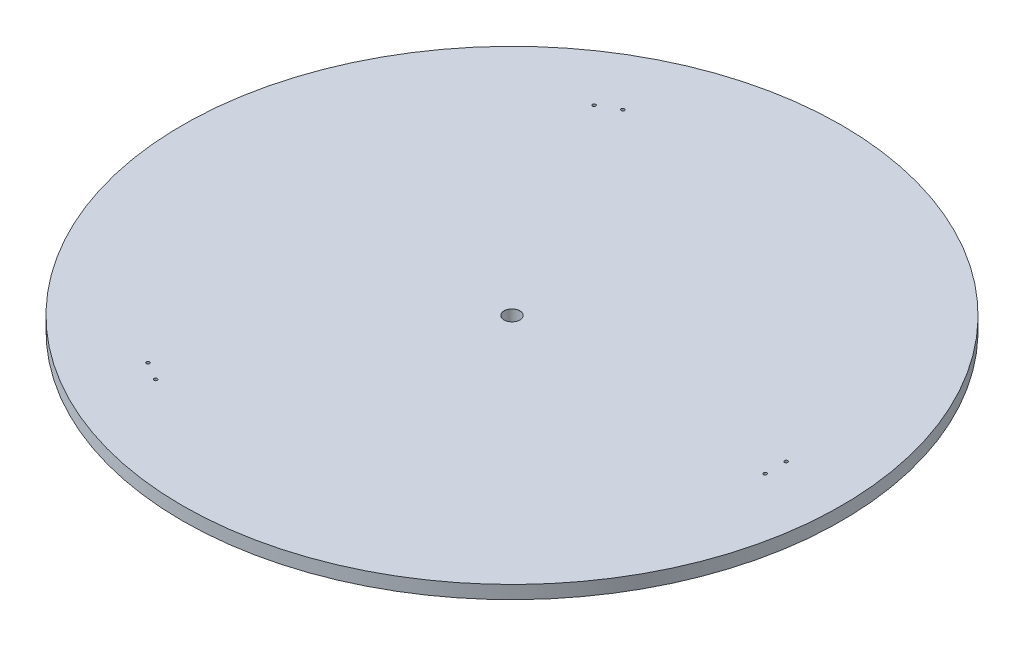
SolidWorks part; units mm, degrees
ref_plane "Plan de face" through (0, 0, 0) normal (0, 0, 1) x (1, 0, 0)
ref_plane "Plan de dessus" through (0, 0, 0) normal (0, 1, 0) x (1, 0, 0)
ref_plane "Plan de droite" through (0, 0, 0) normal (1, 0, 0) x (0, 0, -1)
sketch "Esquisse1" plane through (0, 0, 0) normal (0, 1, 0) x (1, 0, 0)
  circle A0 centre (0, 0) radius 250
  dimension "D1" = 500
extrude "Boss.-Extru.1" add sketch "Esquisse1" along normal mid plane 10
sketch "Esquisse5" plane through (0, 5, 0) normal (0, 1, 0) x (1, 0, 0)
  point P0 (0, 0)
hole_wizard "Dégagement M101" positions "Esquisse5" profile "Esquisse4" hole size "M10" standard "ISO" end condition through all
sketch "Esquisse4" plane through (0, 5, 0) normal (1, 0, 0) x (0, 0, 1)
  line L0 (0, 0) -> (0, 10)
  line L1 (0, 10) -> (6, 10)
  line L2 (6, 10) -> (6, 0.025)
  line L3 (6, 0.025) -> (6.025, 0)
  line L5 (6.025, 0) -> (0, 0)
  line L6 (-6, 0.025) -> (-6.025, 0) construction
  line L11 (0, -6.35) -> (0, 107.95) construction
  dimension "Diamètre du perçage jusqu'au prochain" = 12
  dimension "Profondeur du perçage jusqu'au prochain" = 10
  dimension "Diamètre du fraisage entrant" = 12.05
  dimension "Angle du fraisage entrant" = 90
sketch "Esquisse6" plane through (0, 5, 0) normal (0, 1, 0) x (1, 0, 0)
  line L0 (0, 0) -> (458.2969, 0) construction
  line L1 (0, 0) -> (-167.1022, 289.4294) construction
  line L2 (0, 0) -> (-171.7601, -297.4973) construction
  circle A0 centre (200, 8) radius 1.25
  circle A5 centre (200, -8) radius 1.25
  dimension "D5" = 2.5
  dimension "D3" = 8
  dimension "D4" = 200
  dimension "D1" = 120
  dimension "D2" = 120
extrude "Enlèv. mat.-Extru.1" cut sketch "Esquisse6" against normal through all
pattern_circular "Répétition circulaire1" count 3 over 360 about axis through (0, 0, 0) along (0, 1, 0) of "Enlèv. mat.-Extru.1"
